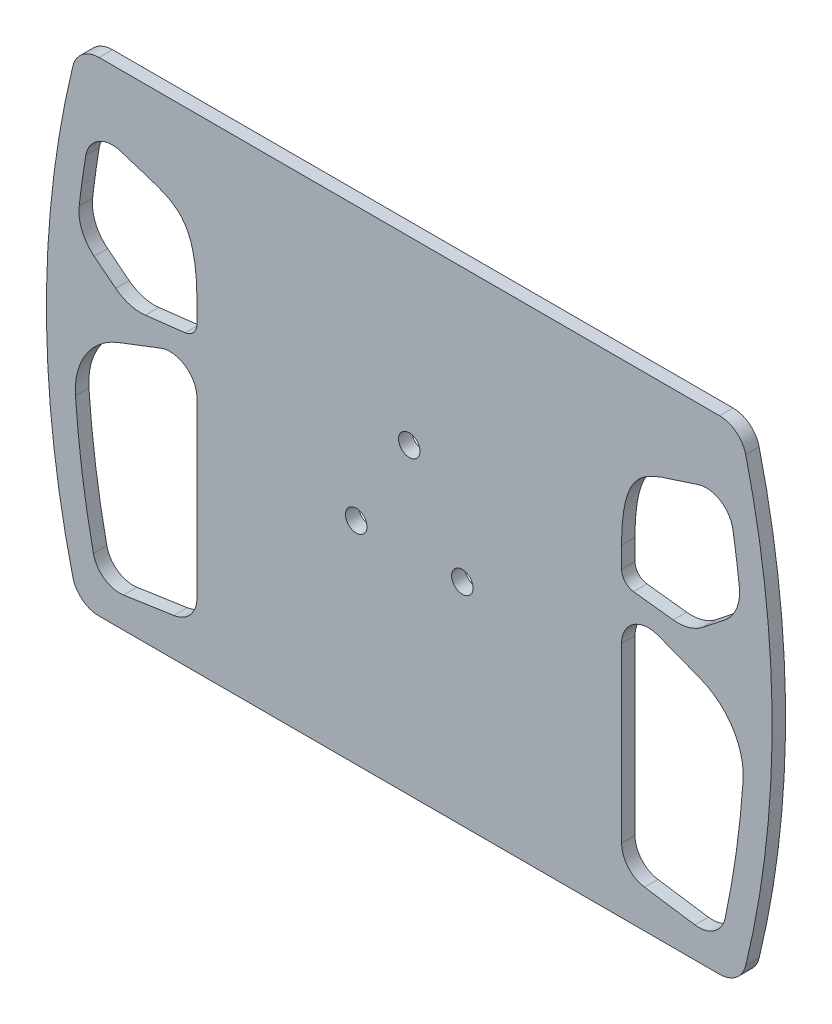
SolidWorks part; units mm, degrees
ref_plane "Front Plane" through (0, 0, 0) normal (0, 0, 1) x (1, 0, 0)
ref_plane "Top Plane" through (0, 0, 0) normal (0, 1, 0) x (1, 0, 0)
ref_plane "Right Plane" through (0, 0, 0) normal (1, 0, 0) x (0, 0, -1)
sketch "Sketch1" plane through (0, 0, 0) normal (0, 0, 1) x (1, 0, 0)
  line L0 (0, 172.3463) -> (0, -176.3137) construction
  line L1 (0, -83) -> (-75, -83) construction
  line L3 (0, 83) -> (-75, 83) construction
  line L4 (-75, -83) -> (-75, 83) construction
  line L7 (115.4542, -90) -> (-115.4542, -90)
  line L9 (115.4542, 90) -> (-115.4542, 90)
  arc A0 (-125.1735, 82.3529) -> (-125.1735, -82.3529) centre (215, 0) ccw
  arc A1 (-125.1735, -82.3529) -> (-115.4542, -90) centre (-115.4542, -80) ccw
  arc A2 (-125.1735, 82.3529) -> (-115.4542, 90) centre (-115.4542, 80) cw
  arc A3 (125.1735, -82.3529) -> (115.4542, -90) centre (115.4542, -80) cw
  arc A4 (125.1735, 82.3529) -> (125.1735, -82.3529) centre (-215, 0) cw
  arc A5 (125.1735, 82.3529) -> (115.4542, 90) centre (115.4542, 80) ccw
  point P0 (0, 0)
  point P6 (0, 0)
  point P17 (0, -90)
  point P25 (0, 90)
  dimension "D5" = 10
  dimension "D4" = 83
  dimension "D6" = 10
  dimension "D1" = 166
  dimension "D2" = 90
  dimension "D3" = 90
  dimension "D7" = 75
extrude "Boss-Extrude1" add sketch "Sketch1" along normal blind 5
sketch "Sketch2" plane through (0, 0, 5) normal (0, 0, 1) x (1, 0, 0)
  circle A0 centre (0, 0) radius 22.8 construction
  circle A1 centre (0, 22.8) radius 4
  circle A2 centre (19.7454, -11.4) radius 4
  circle A3 centre (-19.7454, -11.4) radius 4
  point P6 (0, 0)
  point P11 (0, 0)
  dimension "D1" = 45.6
  dimension "D2" = 8
  dimension "D5" = 8
extrude "Cut-Extrude1" cut sketch "Sketch2" against normal blind 5
sketch "Sketch3" plane through (0, 0, 5) normal (0, 0, 1) x (1, 0, 0)
  line L0 (115.4542, 90) -> (-115.4542, 90) construction
  line L2 (115.4542, 90) -> (-115.4542, 90)
  line L4 (0, 104.8042) -> (0, -107.3413) construction
  line L5 (75, -83) -> (-75, -83) construction
  line L6 (75, -83) -> (75, 83) construction
  line L7 (75, 83) -> (-75, 83) construction
  line L8 (-75, -83) -> (-75, 83) construction
  line L9 (75, -83) -> (-75, 83) construction
  line L10 (75, 83) -> (-75, -83) construction
  line L11 (-75, 30.1129) -> (-75, -74.6191)
  line L12 (-75, -83) -> (-73.5762, -81.074)
  line L13 (75, 30.1129) -> (75, -74.6191)
  arc A1 (-115.4542, 90) -> (-125.1735, 82.3529) centre (-115.4542, 80) ccw construction
  arc A2 (125.1735, 82.3529) -> (115.4542, 90) centre (115.4542, 80) ccw construction
  arc A7 (-115.4542, 90) -> (-125.1735, 82.3529) centre (-115.4542, 80) ccw
  arc A8 (125.1735, 82.3529) -> (115.4542, 90) centre (115.4542, 80) ccw
  arc A12 (-66.6444, -84.483) -> (66.6444, -84.483) centre (0, 315.2857) ccw
  arc A13 (-66.6444, -84.483) -> (-75, -74.6191) centre (-65, -74.6191) cw
  arc A14 (66.6444, -84.483) -> (75, -74.6191) centre (65, -74.6191) ccw
  spline S0 degree 3 poles (-125.1735, 82.3529) (-126.0247, 78.8368) (-111.3864, 67.2925) (-86.0023, 63.9226) (-75, 51.6109) (-75, 30.1129) knots 0 0 0 0 0.156621 0.539301 1 1 1 1
  spline S1 degree 3 poles (125.1735, 82.3529) (126.0247, 78.8368) (111.3864, 67.2925) (86.0023, 63.9226) (75, 51.6109) (75, 30.1129) knots 0 0 0 0 0.156621 0.539301 1 1 1 1
  point P13 (0, 0)
  dimension "D1" = 10
  dimension "D3" = 10
  dimension "D2" = 150
sketch "Sketch4" plane through (0, 0, 5) normal (0, 0, 1) x (1, 0, 0)
  line L0 (-79, -1.5772) -> (-79, -65.9868)
  line L1 (0, 104.8042) -> (0, -107.3413) construction
  line L2 (-106.2977, -78.6484) -> (-87.5398, -75.8797)
  line L3 (-79, 30.1129) -> (-79, -74.6191)
  line L4 (-79, 30.1129) -> (-79, 22.2748)
  line L5 (-117.2131, 25.0143) -> (-109.2361, 18.7094)
  line L6 (-98.1905, 15.5792) -> (-83.4186, 17.3087)
  line L7 (-92.5896, 7.7564) -> (-108.233, 1.74)
  line L8 (106.2977, -78.6484) -> (87.5398, -75.8797)
  line L9 (79, -1.5772) -> (79, -65.9868)
  line L10 (92.5896, 7.7564) -> (108.233, 1.74)
  line L11 (79, 30.1129) -> (79, 22.2748)
  line L12 (98.1905, 15.5792) -> (83.4186, 17.3087)
  line L13 (117.2131, 25.0143) -> (109.2361, 18.7094)
  arc A0 (-79, 22.2748) -> (-83.4186, 17.3087) centre (-84, 22.2748) cw
  arc A1 (-107.1656, 63.7122) -> (-120.368, 55.9311) centre (-110.5043, 54.286) ccw
  arc A2 (-115.4542, 80) -> (-115.4542, -80) centre (215, 0) ccw
  arc A3 (-120.368, 55.9311) -> (-122.8155, 38.48) centre (215, 0) ccw
  arc A4 (-79, -65.9868) -> (-87.5398, -75.8797) centre (-89, -65.9868) cw
  arc A5 (-117.5384, -70.8391) -> (-106.2977, -78.6484) centre (-107.7579, -68.7556) ccw
  arc A6 (-122.8155, 38.48) -> (-117.2131, 25.0143) centre (-107.9118, 36.7824) ccw
  arc A7 (-109.2361, 18.7094) -> (-98.1905, 15.5792) centre (-99.9348, 30.4775) ccw
  arc A9 (-124.2002, -23.3076) -> (-117.5384, -70.8391) centre (215, 0) ccw
  arc A10 (-115.4542, 80) -> (-115.4542, -80) centre (215, 0) ccw
  arc A11 (-120.368, 55.9311) -> (-122.8155, 38.48) centre (215, 0) ccw
  arc A12 (-108.233, 1.74) -> (-124.2002, -23.3076) centre (-99.259, -21.5938) ccw
  arc A13 (-92.5896, 7.7564) -> (-79, -1.5772) centre (-89, -1.5772) cw
  arc A14 (108.233, 1.74) -> (124.2002, -23.3076) centre (99.259, -21.5938) cw
  arc A15 (124.2002, -23.3076) -> (117.5384, -70.8391) centre (-215, 0) cw
  arc A16 (117.5384, -70.8391) -> (106.2977, -78.6484) centre (107.7579, -68.7556) cw
  arc A17 (79, -65.9868) -> (87.5398, -75.8797) centre (89, -65.9868) ccw
  arc A18 (92.5896, 7.7564) -> (79, -1.5772) centre (89, -1.5772) ccw
  arc A19 (79, 22.2748) -> (83.4186, 17.3087) centre (84, 22.2748) ccw
  arc A20 (109.2361, 18.7094) -> (98.1905, 15.5792) centre (99.9348, 30.4775) cw
  arc A21 (122.8155, 38.48) -> (117.2131, 25.0143) centre (107.9118, 36.7824) cw
  arc A22 (120.368, 55.9311) -> (122.8155, 38.48) centre (-215, 0) cw
  arc A23 (107.1656, 63.7122) -> (120.368, 55.9311) centre (110.5043, 54.286) cw
  spline S0 degree 3 poles (107.1656, 63.7122) (105.4217, 63.0946) (103.7337, 62.5539) (100.6072, 61.583) (99.1592, 61.1479) (96.4103, 60.2885) (95.1094, 59.8641) (92.6758, 58.9779) (91.5435, 58.5162) (89.458, 57.5168) (88.5052, 56.9799) (86.7636, 55.7912) (85.9741, 55.1405) (84.5173, 53.6544) (83.8485, 52.8184) (82.6079, 50.8519) (82.0363, 49.7199) (81.0105, 47.0564) (80.5572, 45.5249) (79.8071, 41.9901) (79.5106, 39.9872) (79.107, 35.4562) (79, 32.9282) (79, 30.1129) knots 0.308065 0.308065 0.308065 0.308065 0.375 0.375 0.4375 0.4375 0.5 0.5 0.5625 0.5625 0.625 0.625 0.6875 0.6875 0.75 0.75 0.8125 0.8125 0.875 0.875 0.9375 0.9375 1 1 1 1
  spline S5 degree 3 poles (784.8622, -2768.1192) (36.6498, 180.6068) (-130.257, 110.6815) (-129.2557, 80.4759) (-129.1404, 79.8024) (-128.7813, 78.5456) (-128.5387, 77.9613) (-127.9772, 76.8764) (-127.6581, 76.3748) (-126.6281, 74.9642) (-125.8459, 74.1454) (-124.1875, 72.6408) (-123.3086, 71.9564) (-121.517, 70.6834) (-120.6042, 70.0957) (-118.8158, 69.0084) (-117.9262, 68.5006) (-115.2738, 67.0722) (-113.5286, 66.2471) (-108.4039, 64.0616) (-105.1363, 62.9895) (-100.6072, 61.583) (-99.1592, 61.1479) (-96.4103, 60.2885) (-95.1094, 59.8641) (-92.6758, 58.9779) (-91.5435, 58.5162) (-89.458, 57.5168) (-88.5052, 56.9799) (-86.7636, 55.7912) (-85.9741, 55.1405) (-84.5173, 53.6544) (-83.8485, 52.8184) (-82.6079, 50.8519) (-82.0363, 49.7199) (-81.0105, 47.0564) (-80.5572, 45.5249) (-79.8071, 41.9901) (-79.5106, 39.9872) (-71.6004, -48.8312) (-202.1466, -518.3541) (-1158.0111, -2767.2839) knots -0.645187 -0.645187 -0.645187 -0.645187 0.015625 0.015625 0.03125 0.03125 0.046875 0.046875 0.0625 0.0625 0.09375 0.09375 0.125 0.125 0.15625 0.15625 0.1875 0.1875 0.25 0.25 0.375 0.375 0.4375 0.4375 0.5 0.5 0.5625 0.5625 0.625 0.625 0.6875 0.6875 0.75 0.75 0.8125 0.8125 0.875 0.875 0.9375 0.9375 3.325262 3.325262 3.325262 3.325262 only from (-129.0612, 83.2941) to (-79, 30.1129)
  spline S6 degree 3 poles (-107.1656, 63.7122) (-105.4217, 63.0946) (-103.7337, 62.5539) (-100.6072, 61.583) (-99.1592, 61.1479) (-96.4103, 60.2885) (-95.1094, 59.8641) (-92.6758, 58.9779) (-91.5435, 58.5162) (-89.458, 57.5168) (-88.5052, 56.9799) (-86.7636, 55.7912) (-85.9741, 55.1405) (-84.5173, 53.6544) (-83.8485, 52.8184) (-82.6079, 50.8519) (-82.0363, 49.7199) (-81.0105, 47.0564) (-80.5572, 45.5249) (-79.8071, 41.9901) (-79.5106, 39.9872) (-79.107, 35.4562) (-79, 32.9282) (-79, 30.1129) knots 0.308065 0.308065 0.308065 0.308065 0.375 0.375 0.4375 0.4375 0.5 0.5 0.5625 0.5625 0.625 0.625 0.6875 0.6875 0.75 0.75 0.8125 0.8125 0.875 0.875 0.9375 0.9375 1 1 1 1
  dimension "D3" = 10
  dimension "D5" = 10
  dimension "D4" = 10
  dimension "D6" = 15
  dimension "D7" = 15
  dimension "D8" = 5
  dimension "D10" = 25
  dimension "D11" = 10
  dimension "D2" = 4
  dimension "D12" = 43.8155
  dimension "D13" = 38.2131
  dimension "D1" = 10
  dimension "D9" = 10
extrude "Cut-Extrude4" cut sketch "Sketch4" against normal blind 35 contours L10 A18 L9 A17 L8 A16 A15 A14 | A13 L7 A12 A9 A5 L2 A4 L0 | S6 A1 A3 A6 L5 A7 L6 A0 L4 | S0 L11 A19 L12 A20 L13 A21 A22 A23
sketch "Sketch5" plane through (0, 0, 5) normal (0, 0, 1) x (1, 0, 0)
  line L0 (116.8065, 63.9443) -> (127.9011, 67.8738)
  line L1 (82, 18.8107) -> (82, 4.9036)
  line L2 (85, -93) -> (115.4542, -93)
  line L3 (-83.7674, 20.2884) -> (-83.6744, 20.2993)
  line L8 (0, 60.8844) -> (0, -68.7556) construction
  line L9 (0, 104.8042) -> (0, -107.3413) construction
  line L10 (115.3528, 27.3679) -> (107.3758, 21.063)
  line L11 (-82, -65.9868) -> (-82, -1.5772)
  line L12 (-106.7357, -75.6806) -> (-87.9778, -72.9118)
  line L13 (-91.5127, 4.9563) -> (-107.1561, -1.06)
  line L15 (-106.7357, -75.6806) -> (-87.9778, -72.9118)
  line L16 (-91.5127, 4.9563) -> (-107.1561, -1.06)
  line L17 (98.5394, 18.5589) -> (83.7674, 20.2884)
  line L19 (91.5127, 4.9563) -> (107.1561, -1.06)
  line L20 (106.7357, -75.6806) -> (87.9778, -72.9118)
  line L22 (-82, 4.9036) -> (-82, 18.8094)
  line L25 (-82, -72.4676) -> (-82, -90)
  line L26 (-115.4542, -93) -> (115.4542, -93)
  line L27 (-115.4542, -93) -> (-85, -93)
  line L28 (82, -72.4676) -> (82, -90)
  line L30 (-116.8065, 63.9443) -> (-127.9011, 67.8738)
  line L92 (-82, 22.2748) -> (-82, 30.1129)
  line L93 (-98.5394, 18.5589) -> (-83.7674, 20.2884)
  line L94 (-115.3528, 27.3679) -> (-107.3758, 21.063)
  line L96 (-98.5394, 18.5589) -> (-83.7674, 20.2884)
  line L97 (-115.3528, 27.3679) -> (-107.3758, 21.063)
  arc A0 (-127.9011, 67.8738) -> (-131.8504, 65.6035) centre (-128.9026, 65.0459) ccw
  arc A1 (-116.8065, 63.9443) -> (-115.6169, 59.0673) centre (-117.8081, 61.1164) cw
  arc A2 (-83.6744, 20.2993) -> (-82, 18.8094) centre (-83.5, 18.8094) cw
  arc A3 (-84.4706, 3.7599) -> (-82, 4.9036) centre (-83.5, 4.9036) ccw
  arc A4 (-82, -72.4676) -> (-84.4706, -71.3239) centre (-83.5, -72.4676) ccw
  arc A5 (-82, -90) -> (-85, -93) centre (-85, -90) cw
  arc A6 (82, -90) -> (85, -93) centre (85, -90) ccw
  arc A7 (116.8065, 63.9443) -> (115.6169, 59.0673) centre (117.8081, 61.1164) ccw
  arc A8 (127.9011, 67.8738) -> (131.8504, 65.6035) centre (128.9026, 65.0459) cw
  arc A9 (83.7143, 20.2953) -> (82, 18.8107) centre (83.5, 18.8107) ccw
  arc A10 (84.4706, 3.7599) -> (82, 4.9036) centre (83.5, 4.9036) cw
  arc A11 (84.4706, -71.3239) -> (82, -72.4676) centre (83.5, -72.4676) ccw
  arc A14 (117.4089, 55.4375) -> (119.8347, 38.1405) centre (-215, 0) cw
  arc A15 (-128.0892, 83.0588) -> (-128.0892, -83.0588) centre (215, 0) ccw
  arc A16 (-131.8504, 65.6035) -> (-128.0892, -83.0588) centre (215, 0) ccw
  arc A17 (115.6169, 59.0673) -> (117.4089, 55.4375) centre (110.5043, 54.286) cw
  arc A18 (-82, -1.5772) -> (-91.5127, 4.9563) centre (-89, -1.5772) ccw
  arc A19 (-87.9778, -72.9118) -> (-82, -65.9868) centre (-89, -65.9868) ccw
  arc A20 (-114.6043, -70.2141) -> (-106.7357, -75.6806) centre (-107.7579, -68.7556) ccw
  arc A21 (-121.2072, -23.1019) -> (-114.6043, -70.2141) centre (215, 0) ccw
  arc A22 (-107.1561, -1.06) -> (-121.2072, -23.1019) centre (-99.259, -21.5938) ccw
  arc A23 (-84.4706, 3.7599) -> (-91.5127, 4.9563) centre (-89, -1.5772) ccw
  arc A24 (-87.9778, -72.9118) -> (-84.4706, -71.3239) centre (-89, -65.9868) ccw
  arc A25 (-114.6043, -70.2141) -> (-106.7357, -75.6806) centre (-107.7579, -68.7556) ccw
  arc A26 (-121.2072, -23.1019) -> (-114.6043, -70.2141) centre (215, 0) ccw
  arc A27 (-107.1561, -1.06) -> (-121.2072, -23.1019) centre (-99.259, -21.5938) ccw
  arc A28 (119.8347, 38.1405) -> (115.3528, 27.3679) centre (107.9118, 36.7824) cw
  arc A29 (107.3758, 21.063) -> (98.5394, 18.5589) centre (99.9348, 30.4775) cw
  arc A30 (83.7674, 20.2884) -> (83.7143, 20.2953) centre (84, 22.2748) cw
  arc A31 (107.1561, -1.06) -> (121.2072, -23.1019) centre (99.259, -21.5938) cw
  arc A32 (121.2072, -23.1019) -> (114.6043, -70.2141) centre (-215, 0) cw
  arc A33 (114.6043, -70.2141) -> (106.7357, -75.6806) centre (107.7579, -68.7556) cw
  arc A34 (87.9778, -72.9118) -> (84.4706, -71.3239) centre (89, -65.9868) cw
  arc A35 (84.4706, 3.7599) -> (91.5127, 4.9563) centre (89, -1.5772) cw
  arc A36 (131.8504, 65.6035) -> (128.0892, -83.0588) centre (-215, 0) cw
  arc A43 (115.4542, -93) -> (128.0892, -83.0588) centre (115.4542, -80) ccw
  arc A44 (-128.0892, -83.0588) -> (-115.4542, -93) centre (-115.4542, -80) ccw
  arc A45 (115.4542, -93) -> (128.0892, -83.0588) centre (115.4542, -80) ccw
  arc A46 (-128.0892, -83.0588) -> (-115.4542, -93) centre (-115.4542, -80) ccw
  arc A185 (-83.7674, 20.2884) -> (-82, 22.2748) centre (-84, 22.2748) ccw
  arc A186 (-107.3758, 21.063) -> (-98.5394, 18.5589) centre (-99.9348, 30.4775) ccw
  arc A187 (-119.8347, 38.1405) -> (-115.3528, 27.3679) centre (-107.9118, 36.7824) ccw
  arc A188 (-108.1672, 60.8844) -> (-117.4089, 55.4375) centre (-110.5043, 54.286) ccw
  arc A189 (-117.4089, 55.4375) -> (-119.8347, 38.1405) centre (215, 0) ccw
  arc A191 (-107.3758, 21.063) -> (-98.5394, 18.5589) centre (-99.9348, 30.4775) ccw
  arc A192 (-119.8347, 38.1405) -> (-115.3528, 27.3679) centre (-107.9118, 36.7824) ccw
  arc A193 (-115.6169, 59.0673) -> (-117.4089, 55.4375) centre (-110.5043, 54.286) ccw
  arc A194 (-117.4089, 55.4375) -> (-119.8347, 38.1405) centre (215, 0) ccw
  spline S38 degree 3 poles (913.4217, -65.4443) (-178.4662, -120.6273) (-77.5097, -36.2196) (-82.2951, 37.7257) (-82.4898, 39.6148) (-82.9629, 42.4272) (-83.1513, 43.361) (-83.4986, 44.7543) (-83.6252, 45.2174) (-83.905, 46.1406) (-84.058, 46.5995) (-84.5591, 47.9528) (-84.9499, 48.8289) (-85.663, 50.0847) (-85.9237, 50.4959) (-86.4866, 51.2804) (-86.7885, 51.6531) (-87.4347, 52.3583) (-87.7787, 52.691) (-88.5078, 53.3173) (-88.8953, 53.6124) (-90.089, 54.4318) (-90.9275, 54.894) (-92.6535, 55.7217) (-93.5413, 56.0868) (-95.3434, 56.7646) (-96.2544, 57.0753) (-98.9985, 57.9697) (-100.8437, 58.5176) (-155.7405, 75.4959) (-203.823, 107.2425) (43.4333, 1049.3006) knots -4.621308 -4.621308 -4.621308 -4.621308 0.125 0.125 0.25 0.25 0.3125 0.3125 0.34375 0.34375 0.375 0.375 0.4375 0.4375 0.46875 0.46875 0.5 0.5 0.53125 0.53125 0.5625 0.5625 0.625 0.625 0.6875 0.6875 0.75 0.75 0.875 0.875 4.482662 4.482662 4.482662 4.482662 only from (-82, 30.1129) to (-108.1672, 60.8844)
  point P86 (82, -93)
  point P93 (82, 22.2748)
  point P96 (82, -1.5772)
  point P99 (82, -65.9868)
  dimension "D5" = 3
  dimension "D6" = 3
  dimension "D7" = 1.5
  dimension "D8" = 1.5
  dimension "D9" = 1.5
  dimension "D10" = 3
  dimension "D11" = 3
  dimension "D12" = 3
  dimension "D13" = 3
  dimension "D14" = 1.5
  dimension "D15" = 1.5
  dimension "D16" = 1.5
  dimension "D1" = 3
  dimension "D2" = 3
  dimension "D3" = 3
  dimension "D4" = 3
